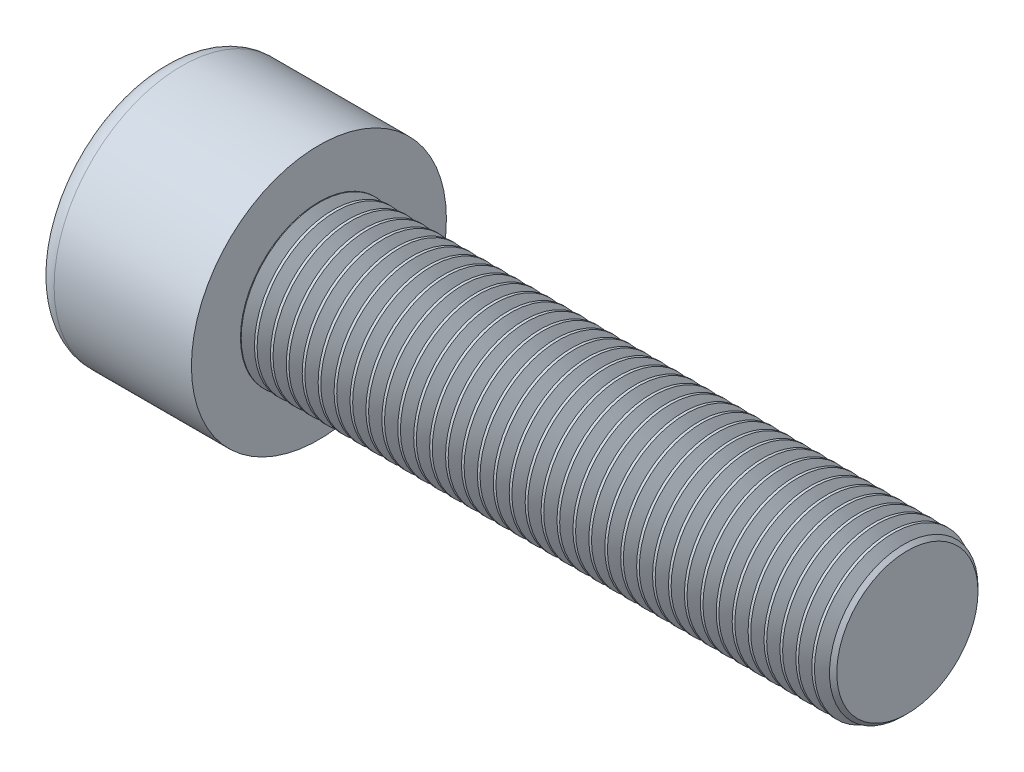
SolidWorks part; units mm, degrees
ref_plane "Front" through (0, 0, 0) normal (0, 0, 1) x (1, 0, 0)
ref_plane "Top" through (0, 0, 0) normal (0, 1, 0) x (1, 0, 0)
ref_plane "Right" through (0, 0, 0) normal (1, 0, 0) x (0, 0, -1)
sketch "Sketch1" plane through (0, 0, 0) normal (1, 0, 0) x (0, 0, -1)
  circle A0 centre (0, 0) radius 6.5
  dimension "dk" = 13
extrude "BaseHead" add sketch "Sketch1" along normal blind 8
sketch "Sketch2" plane through (8, 0, 0) normal (1, 0, 0) x (0, 0, -1)
  circle A0 centre (0, 0) radius 4
  dimension "d" = 8
extrude "BaseBody" add sketch "Sketch2" along normal blind 30
cosmetic thread "ThreadCosmetic1" [suppressed] parameters "b"=30, "D2"=6.647
sketch "Sketch3" plane through (0, 0, 0) normal (1, 0, 0) x (0, 0, -1)
  line L1 (3.4641, 0) -> (1.7321, 3)
  line L2 (1.7321, 3) -> (-1.7321, 3)
  line L3 (-1.7321, 3) -> (-3.4641, 0)
  line L4 (-3.4641, 0) -> (-1.7321, -3)
  line L5 (-1.7321, -3) -> (1.7321, -3)
  line L6 (1.7321, -3) -> (3.4641, 0)
  circle A0 centre (0, 0) radius 3 construction
  dimension "s" = 6
  dimension "e" = 6.9282
extrude "HexagonSocket" cut sketch "Sketch3" along normal blind 4
sketch "Sketch4" plane through (-4.1961, 0.75, 0) normal (0, 0, 1) x (-1, 0, 0)
  line L0 (-8.1961, 3.75) -> (-9.9282, 0.75)
  line L2 (-9.9282, 0.75) -> (-8.1961, 0.75)
  line L3 (-8.1961, 0.75) -> (-8.1961, 3.75)
  line L4 (-5.0351, 0.75) -> (0.839, 0.75) construction
  line L5 (-42.1961, 0.75) -> (-12.1961, 0.75) construction
  line L6 (-12.1961, 0.75) -> (-4.1961, 0.75) construction
  dimension "m" = 60
revolve "Cut-Revolve1" cut sketch "Sketch4" angle 360 about L4
fillet "HeadFillet" [suppressed] radius 0.4
fillet "TopFillet" radius 1 1 edges at (0, 0, -6.5)
chamfer "Chamfer1" distance 0.4 angle 45 1 edges at (38, 0, -4)
sketch "Sketch5" plane through (0, 0, 0) normal (0, 0, 1) x (1, 0, 0)
  line L0 (37.6, 3.4141) -> (37.9383, 4)
  line L1 (37.9383, 4) -> (37.9383, 4.6765)
  line L2 (37.9383, 4.6765) -> (37.2618, 4.6765)
  line L3 (37.2618, 4.6765) -> (37.2618, 4)
  line L4 (37.2618, 4) -> (37.6, 3.4141)
  line L5 (0, 0) -> (7.8886, 0) construction
  line L6 (37.6, -4) -> (37.6, 4) construction
  dimension "D1" = 8
  dimension "D2" = 0.6765
revolve "Cut-Revolve10" cut sketch "Sketch5" angle 360 about L5
pattern_linear "LPattern10" count 37 spacing 0.8118 along (-1, 0, 0) of "Cut-Revolve10"
equation "\"r1@TopFillet\" = \"d@Sketch2\" / 8"
equation "\"D1@Chamfer1\" = \"r@HeadFillet\""
equation "\"D1@Sketch5\" = \"d@Sketch2\""
equation "\"D2@Sketch5\" =  ( \"d@Sketch2\" - \"D2@ThreadCosmetic1\" )  / 2"
equation "\"D3@LPattern10\" = \"D2@Sketch5\" * 1.2"
equation "\"D1@LPattern10\" = \"b@ThreadCosmetic1\" / \"D3@LPattern10\""
